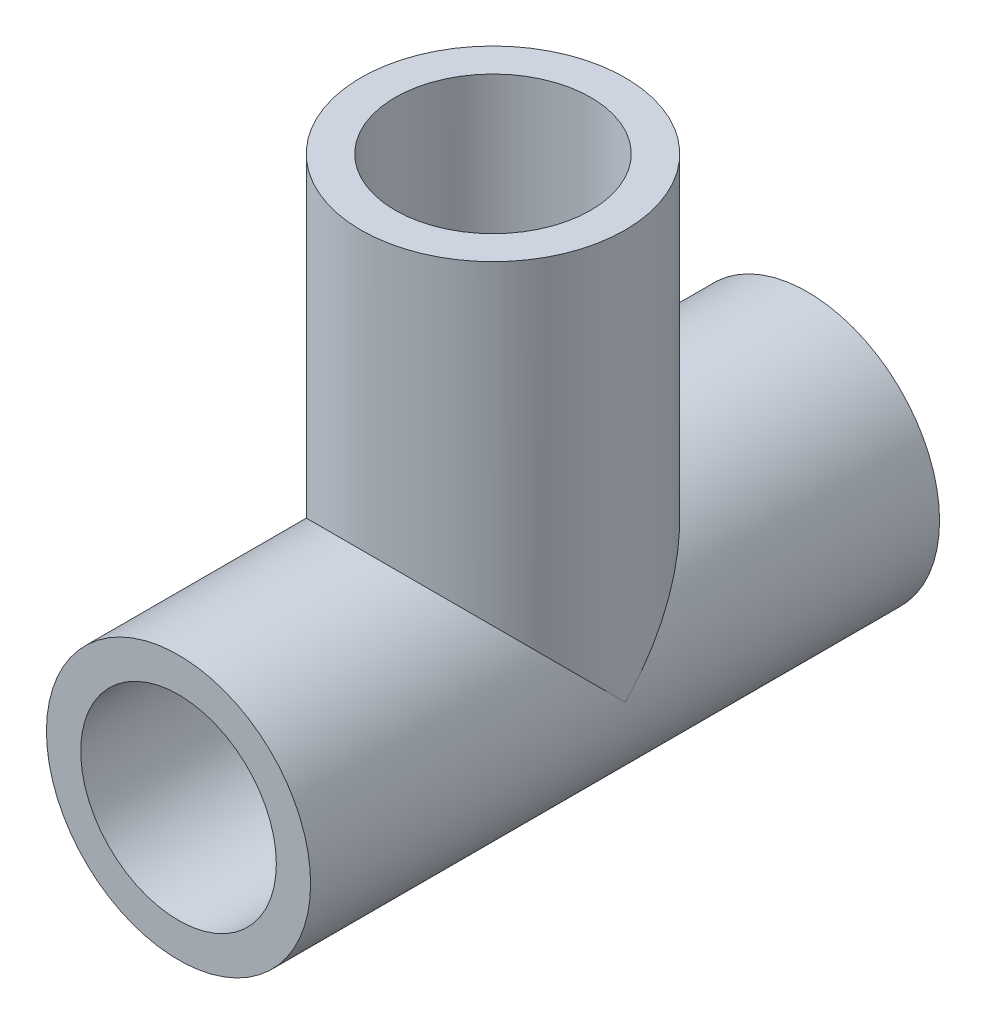
SolidWorks part; units mm, degrees
material "PVC Rigid"
ref_plane "Front Plane" through (0, 0, 0) normal (0, 0, 1) x (1, 0, 0)
ref_plane "Top Plane" through (0, 0, 0) normal (0, 1, 0) x (1, 0, 0)
ref_plane "Right Plane" through (0, 0, 0) normal (1, 0, 0) x (0, 0, -1)
sketch "Sketch1" plane through (0, 0, 0) normal (0, 0, 1) x (1, 0, 0)
  circle A0 centre (0, 0) radius 10.668
  circle A2 centre (0, 0) radius 7.8994
  dimension "D1" = 21.336
  dimension "D2" = 15.7988
extrude "Boss-Extrude1" add sketch "Sketch1" along normal blind 50.8
sketch "Sketch2" plane through (0, 0, 0) normal (0, 1, 0) x (1, 0, 0)
  line L0 (-10.668, -25.4) -> (10.668, -25.4) construction
  line L1 (-10.668, 0) -> (-10.668, -50.8) construction
  line L2 (10.668, -50.8) -> (10.668, 0) construction
  line L3 (0, 0) -> (0, -50.8) construction
  line L4 (-10.668, -50.8) -> (10.668, -50.8) construction
  circle A0 centre (0, -25.4) radius 10.668
  circle A1 centre (0, -25.4) radius 7.8994
  point P15 (0, -25.4)
  dimension "D1" = 21.336
  dimension "D2" = 15.7988
extrude "Boss-Extrude2" add sketch "Sketch2" along normal blind 33.02
sketch "Sketch3" plane through (0, 0, 50.8) normal (0, 0, 1) x (1, 0, 0)
  circle A0 centre (0, 0) radius 7.8994
extrude "Cut-Extrude1" cut sketch "Sketch3" against normal through all
sketch "Sketch4" plane through (0, 33.02, 0) normal (0, 1, 0) x (1, 0, 0)
  circle A0 centre (0, -25.4) radius 7.8994
extrude "Cut-Extrude2" cut sketch "Sketch4" against normal up to next
